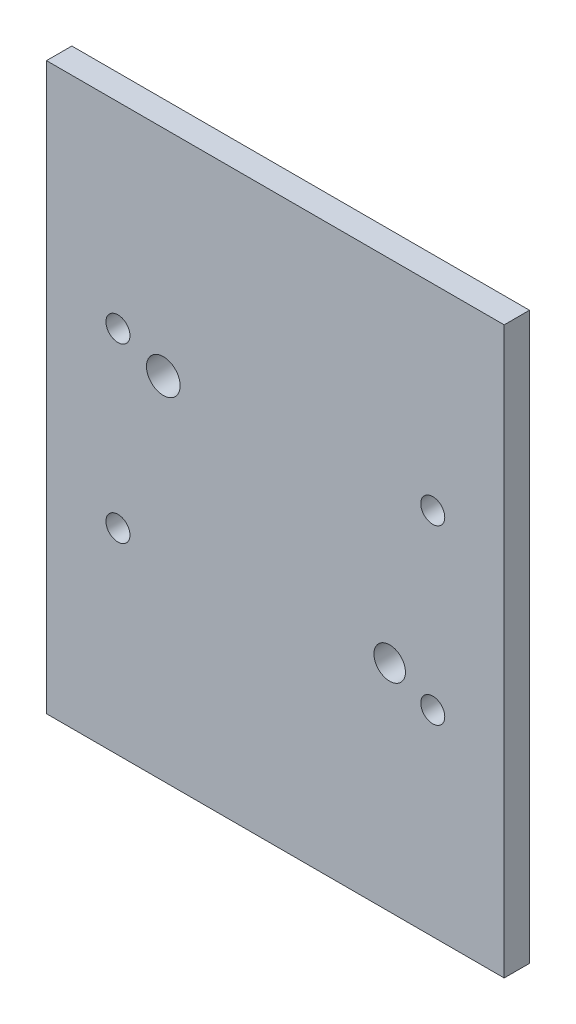
SolidWorks part; units mm, degrees
ref_plane "Front Plane" through (0, 0, 0) normal (0, 0, 1) x (1, 0, 0)
ref_plane "Top Plane" through (0, 0, 0) normal (0, 1, 0) x (1, 0, 0)
ref_plane "Right Plane" through (0, 0, 0) normal (1, 0, 0) x (0, 0, -1)
sketch "Sketch1" plane through (0, 0, 0) normal (0, 0, 1) x (1, 0, 0)
  line L0 (21.5265, 0) -> (21.5265, -53.213)
  line L1 (21.5265, 0) -> (-21.5265, 0)
  line L2 (0, 0) -> (0, -53.213)
  line L3 (21.5265, -53.213) -> (-21.5265, -53.213)
  line L4 (-21.5265, 0) -> (-21.5265, -53.213)
extrude "Boss-Extrude1" add sketch "Sketch1" along normal blind 2.3813 contours L4 L3 L0 L1
hole_wizard "#4-40 Tapped Hole1" positions "Sketch2" profile "Sketch3" tap size "#4-40" standard "ANSI Inch" end condition through all
sketch "Sketch2" plane through (0, 0, 2.3813) normal (0, 0, 1) x (1, 0, 0)
  point P0 (-14.8082, -18.4804)
  point P2 (14.8082, -18.4804)
  point P4 (-14.8082, -34.7326)
  point P6 (14.8082, -34.7326)
  point P9 (0, 0)
  point P10 (0, 0)
  point P11 (0, 0)
  point P12 (0, 0)
  point P13 (0, 0)
  point P14 (0, 0)
  point P15 (0, 0)
  point P16 (0, 0)
  point P17 (0, 0)
  point P18 (0, 0)
  point P19 (0, 0)
  point P20 (0, 0)
  point P21 (0, 0)
sketch "Sketch3" plane through (-14.8082, -18.4804, 2.3813) normal (1, 0, 0) x (0, -1, 0)
  line L0 (0, 0) -> (0, 2.3812)
  line L1 (0, 2.3812) -> (1.1303, 2.3812)
  line L2 (1.1303, 2.3812) -> (1.1303, 0)
  line L5 (1.1303, 0) -> (0, 0)
  line L11 (0, -6.35) -> (0, 107.95) construction
  dimension "Thru Tap Drill Dia." = 2.2606
  dimension "Thru Tap Drill Depth" = 2.3813
cosmetic thread "Hole Thread1" parameters "D2"=2.8448
cosmetic thread "Hole Thread2" parameters "D2"=2.8448
cosmetic thread "Hole Thread3" parameters "D2"=2.8448
cosmetic thread "Hole Thread4" parameters "D2"=2.8448
sketch "Sketch5" plane through (0, 0, 2.3813) normal (0, 0, 1) x (1, 0, 0)
  circle A0 centre (-10.5386, -20.2029) radius 1.5832
  circle A1 centre (10.7581, -32.9369) radius 1.4819
extrude "Cut-Extrude1" cut sketch "Sketch5" against normal through all
